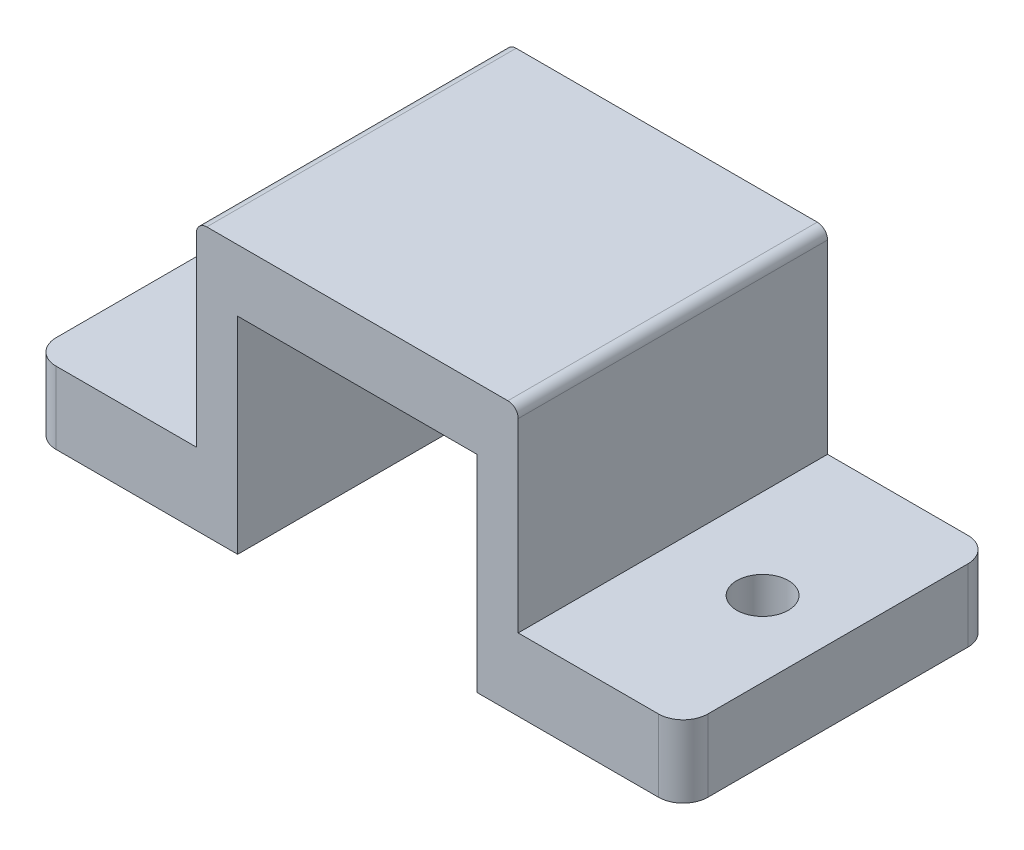
SolidWorks part; units mm, degrees
ref_plane "Front Plane" through (0, 0, 0) normal (0, 0, 1) x (1, 0, 0)
ref_plane "Top Plane" through (0, 0, 0) normal (0, 1, 0) x (1, 0, 0)
ref_plane "Right Plane" through (0, 0, 0) normal (1, 0, 0) x (0, 0, -1)
sketch "Sketch1" plane through (0, 0, 0) normal (0, 0, 1) x (1, 0, 0)
  line L0 (-5.8, 0) -> (-5.8, 10)
  line L1 (5.8, 0) -> (5.8, 10)
  line L2 (0, 0) -> (0, 2.8841) construction
  line L3 (-2.2945, 0) -> (2.1033, 0) construction
  line L4 (-5.8, 10) -> (5.8, 10)
  line L5 (-7.8, 0) -> (-7.8, 10)
  line L6 (-7.8, 10) -> (-7.8, 12.5)
  line L7 (-7.3, 13) -> (5.8571, 13)
  line L8 (7.8, 0) -> (7.8, 12.5)
  line L9 (5.8571, 13) -> (7.3, 13)
  line L10 (7.8, 0) -> (5.8, 0)
  line L11 (-7.8, 0) -> (-5.8, 0)
  arc A0 (7.8, 12.5) -> (7.3, 13) centre (7.3, 12.5) ccw
  arc A1 (-7.8, 12.5) -> (-7.3, 13) centre (-7.3, 12.5) cw
  dimension "D7" = 0.5
  dimension "D1" = 5.8
  dimension "D2" = 5.8
  dimension "D3" = 10
  dimension "D4" = 2
  dimension "D5" = 3
  dimension "D6" = 2
extrude "Boss-Extrude1" add sketch "Sketch1" along normal mid plane 15
sketch "Sketch3" plane through (0, 0, 0) normal (0, 1, 0) x (1, 0, 0)
  line L0 (7.8, 7.5) -> (14.6, 7.5)
  line L1 (15.8, -6.3) -> (15.8, 6.3)
  line L2 (7.8, -7.5) -> (14.6, -7.5)
  line L4 (5.8, -7.5) -> (5.8, 7.5) construction
  line L5 (15.8, 0) -> (8.5, 0) construction
  line L6 (0, 0) -> (0, 4.5471) construction
  line L7 (7.8, 7.5) -> (7.8, -7.5)
  line L8 (7.8, 7.5) -> (14.6, 7.5)
  line L9 (7.8, -7.5) -> (14.6, -7.5)
  line L10 (-15.8, 0) -> (-8.5, 0) construction
  line L11 (-7.8, -7.5) -> (-14.6, -7.5)
  line L12 (-7.8, 7.5) -> (-14.6, 7.5)
  line L13 (-7.8, 7.5) -> (-7.8, -7.5)
  line L14 (-7.8, -7.5) -> (-14.6, -7.5)
  line L15 (-15.8, -6.3) -> (-15.8, 6.3)
  line L16 (-7.8, 7.5) -> (-14.6, 7.5)
  arc A0 (14.6, -7.5) -> (15.8, -6.3) centre (14.6, -6.3) ccw
  arc A1 (14.6, 7.5) -> (15.8, 6.3) centre (14.6, 6.3) cw
  circle A2 centre (12.15, 0) radius 1.25
  arc A3 (14.6, -7.5) -> (15.8, -6.3) centre (14.6, -6.3) ccw
  arc A4 (14.6, 7.5) -> (15.8, 6.3) centre (14.6, 6.3) cw
  arc A5 (-14.6, 7.5) -> (-15.8, 6.3) centre (-14.6, 6.3) ccw
  arc A6 (-14.6, -7.5) -> (-15.8, -6.3) centre (-14.6, -6.3) cw
  circle A7 centre (-12.15, 0) radius 1.25
  arc A8 (-14.6, 7.5) -> (-15.8, 6.3) centre (-14.6, 6.3) ccw
  arc A9 (-14.6, -7.5) -> (-15.8, -6.3) centre (-14.6, -6.3) cw
  dimension "D2" = 1.2
  dimension "D3" = 3.65
  dimension "D1" = 10
extrude "Boss-Extrude2" add sketch "Sketch3" along normal blind 3.5 contours A6 L11 L13 L12 A5 L15 A7 | A1 L0 L7 L2 A0 L1 A2
